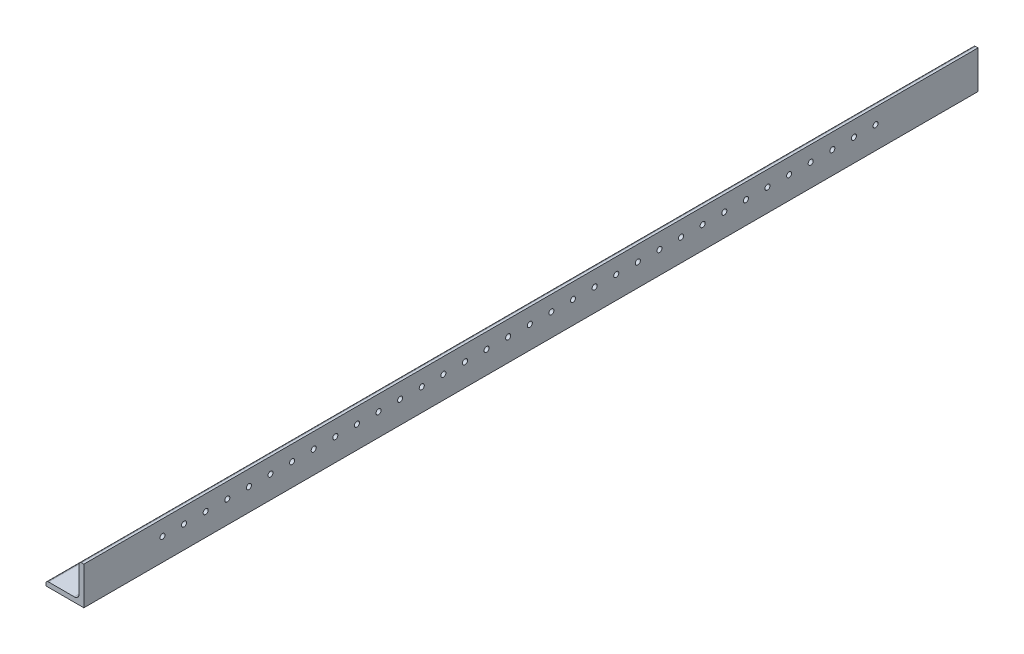
SolidWorks part; units mm, degrees
ref_plane "Front Plane" through (0, 0, 0) normal (0, 0, 1) x (1, 0, 0)
ref_plane "Top Plane" through (0, 0, 0) normal (0, 1, 0) x (1, 0, 0)
ref_plane "Right Plane" through (0, 0, 0) normal (1, 0, 0) x (0, 0, -1)
sketch "Sketch0" plane through (0, 0, 0) normal (0, 0, 1) x (1, 0, 0)
  line L0 (-12.7, -12.7) -> (12.7, -12.7)
  line L1 (12.7, -12.7) -> (12.7, 12.7)
  line L2 (12.7, 0) -> (0, 0) construction
  line L3 (0, 0) -> (0, -12.7) construction
  line L4 (9.525, -6.35) -> (9.525, 12.7) construction
  line L5 (6.35, -9.525) -> (-12.7, -9.525) construction
  arc A0 (9.525, -6.35) -> (6.35, -9.525) centre (6.35, -6.35) cw
  point P3 (8.5951, -8.5951)
  dimension "Inside Corner Radius" = 3.175
  dimension "Outside Height" = 25.4
  dimension "Inside Height" = 22.225
  dimension "Inside Width" = 22.225
  dimension "Wall Thickness" = 3.175
  dimension "D1" = 3.175
  dimension "Outside Width" = 25.4
sketch "Sketch1" plane through (0, 0, 0) normal (1, 0, 0) x (0, 0, -1)
  line L0 (609.6, 0) -> (-609.6, 0)
  point P4 (0, 0)
  dimension "Length" = 1219.2
sketch "Sketch2" plane through (0, 0, 0) normal (0, 0, 1) x (1, 0, 0)
  line L0 (-12.7, -12.7) -> (12.7, -12.7)
  line L1 (12.7, -12.7) -> (12.7, 12.7)
  line L2 (12.7, 12.7) -> (9.525, 12.7) construction
  line L3 (9.525, 11.1125) -> (9.525, -6.35)
  line L4 (6.35, -9.525) -> (-11.1125, -9.525)
  line L5 (-12.7, -12.7) -> (-12.7, -9.525) construction
  line L6 (11.1125, 12.7) -> (12.7, 12.7)
  line L7 (-12.7, -11.1125) -> (-12.7, -12.7)
  line L8 (12.7, 0) -> (0, 0) construction
  line L9 (0, 0) -> (0, -12.7) construction
  arc A0 (9.525, 11.1125) -> (11.1125, 12.7) centre (11.1125, 11.1125) cw
  arc A1 (-12.7, -11.1125) -> (-11.1125, -9.525) centre (-11.1125, -11.1125) cw
  arc A2 (9.525, -6.35) -> (6.35, -9.525) centre (6.35, -6.35) cw
  dimension "Inside Radius" = 3.175
  dimension "Height" = 25.4
  dimension "Width" = 25.4
  dimension "Thickness" = 3.175
extrude "Boss-Extrude1" add sketch "Sketch2" along normal mid plane 1219.2
sketch "Break Locations" plane through (0, 0, 0) normal (1, 0, 0) x (0, 0, -1)
  line L0 (-583.692, 0) -> (583.692, 0)
  line L1 (-609.6, -12.7) -> (-609.6, 12.7) construction
  line L2 (609.6, -12.7) -> (609.6, 12.7) construction
  point P0 (-588.01, 0)
  point P1 (588.01, 0)
  point P10 (0, 0)
  point P11 (583.692, 0)
  point P13 (-583.692, 0)
  dimension "D1" = 21.59
  dimension "D2" = 21.59
  dimension "D3" = 25.908
sketch "Sketch3" plane through (12.7, 0, 0) normal (1, 0, 0) x (0, 0, -1)
  line L0 (-609.6, -12.7) -> (609.6, -12.7) construction
  line L1 (609.6, 12.7) -> (-9.6, 12.7)
  line L2 (609.6, 12.7) -> (609.6, -12.7)
  line L3 (609.6, -12.7) -> (-9.6, -12.7)
  line L4 (-9.6, 12.7) -> (-9.6, -12.7)
  line L5 (-609.6, -12.7) -> (-609.6, 12.7) construction
  dimension "D1" = 600
extrude "Cut-Extrude2" cut sketch "Sketch3" against normal blind 30.48
sketch "Sketch5" plane through (9.525, 0, 0) normal (-1, 0, 0) x (0, 0, 1)
  line L0 (562.77, 11.1125) -> (562.77, -6.35) construction
  line L1 (609.6, 11.1125) -> (9.6, 11.1125) construction
  line L2 (609.6, 11.1125) -> (609.6, -6.35) construction
  line L3 (609.6, -6.35) -> (9.6, -6.35) construction
  line L4 (72.43, 11.1125) -> (72.43, -6.35) construction
  line L6 (72.43, 2.3812) -> (562.77, 2.3812) construction
  line L7 (78.35, 2.3812) -> (72.43, 2.3812)
  line L8 (556.85, 2.3812) -> (562.77, 2.3812)
  line L9 (72.43, 8.7325) -> (72.43, -3.9675) construction
  circle A0 centre (78.35, 2.3812) radius 1.7
  circle A1 centre (92.85, 2.3812) radius 1.7
  circle A2 centre (107.35, 2.3812) radius 1.7
  circle A3 centre (121.85, 2.3812) radius 1.7
  circle A4 centre (136.35, 2.3812) radius 1.7
  circle A5 centre (150.85, 2.3812) radius 1.7
  circle A6 centre (165.35, 2.3812) radius 1.7
  circle A7 centre (179.85, 2.3812) radius 1.7
  circle A8 centre (194.35, 2.3812) radius 1.7
  circle A9 centre (208.85, 2.3812) radius 1.7
  circle A10 centre (223.35, 2.3812) radius 1.7
  circle A11 centre (237.85, 2.3812) radius 1.7
  circle A12 centre (252.35, 2.3812) radius 1.7
  circle A13 centre (266.85, 2.3812) radius 1.7
  circle A14 centre (281.35, 2.3812) radius 1.7
  circle A15 centre (295.85, 2.3812) radius 1.7
  circle A16 centre (310.35, 2.3812) radius 1.7
  circle A17 centre (324.85, 2.3812) radius 1.7
  circle A18 centre (339.35, 2.3812) radius 1.7
  circle A19 centre (353.85, 2.3812) radius 1.7
  circle A20 centre (368.35, 2.3812) radius 1.7
  circle A21 centre (382.85, 2.3812) radius 1.7
  circle A22 centre (397.35, 2.3812) radius 1.7
  circle A23 centre (411.85, 2.3812) radius 1.7
  circle A24 centre (426.35, 2.3812) radius 1.7
  circle A25 centre (440.85, 2.3812) radius 1.7
  circle A26 centre (455.35, 2.3812) radius 1.7
  circle A27 centre (469.85, 2.3812) radius 1.7
  circle A28 centre (484.35, 2.3812) radius 1.7
  circle A29 centre (498.85, 2.3812) radius 1.7
  circle A30 centre (513.35, 2.3812) radius 1.7
  circle A31 centre (527.85, 2.3812) radius 1.7
  circle A32 centre (542.35, 2.3812) radius 1.7
  circle A33 centre (556.85, 2.3812) radius 1.7
  dimension "D1" = 3.4
  dimension "D3" = 14.5
  dimension "D4" = 46.83
  dimension "D2" = 34
extrude "Cut-Extrude3" cut sketch "Sketch5" against normal through all
sketch "Sketch7" plane through (0, -9.525, 0) normal (0, 1, 0) x (1, 0, 0)
  line L0 (-11.1125, -562.7675) -> (6.35, -562.7675) construction
  line L1 (-11.1125, -609.6) -> (-11.1125, -9.6) construction
  line L2 (-2.3812, -556.85) -> (-2.3812, -562.7675)
  line L3 (6.35, -609.6) -> (6.35, -9.6) construction
  line L5 (-2.3812, -72.4325) -> (-2.3812, -562.7675) construction
  line L6 (-2.3812, -78.35) -> (-2.3812, -72.4325)
  line L8 (-8.7325, -562.7675) -> (3.9675, -562.7675) construction
  line L9 (3.9675, -72.4325) -> (-8.7325, -72.4325) construction
  circle A0 centre (-2.3812, -78.35) radius 1.7
  circle A1 centre (-2.3812, -92.85) radius 1.7
  circle A2 centre (-2.3812, -107.35) radius 1.7
  circle A3 centre (-2.3812, -121.85) radius 1.7
  circle A4 centre (-2.3812, -136.35) radius 1.7
  circle A5 centre (-2.3812, -150.85) radius 1.7
  circle A6 centre (-2.3812, -165.35) radius 1.7
  circle A7 centre (-2.3812, -179.85) radius 1.7
  circle A8 centre (-2.3812, -194.35) radius 1.7
  circle A9 centre (-2.3812, -208.85) radius 1.7
  circle A10 centre (-2.3812, -223.35) radius 1.7
  circle A11 centre (-2.3812, -237.85) radius 1.7
  circle A12 centre (-2.3812, -252.35) radius 1.7
  circle A13 centre (-2.3812, -266.85) radius 1.7
  circle A14 centre (-2.3812, -281.35) radius 1.7
  circle A15 centre (-2.3812, -295.85) radius 1.7
  circle A16 centre (-2.3812, -310.35) radius 1.7
  circle A17 centre (-2.3812, -324.85) radius 1.7
  circle A18 centre (-2.3812, -339.35) radius 1.7
  circle A19 centre (-2.3812, -353.85) radius 1.7
  circle A20 centre (-2.3812, -368.35) radius 1.7
  circle A21 centre (-2.3812, -382.85) radius 1.7
  circle A22 centre (-2.3812, -397.35) radius 1.7
  circle A23 centre (-2.3812, -411.85) radius 1.7
  circle A24 centre (-2.3812, -426.35) radius 1.7
  circle A25 centre (-2.3812, -440.85) radius 1.7
  circle A26 centre (-2.3812, -455.35) radius 1.7
  circle A27 centre (-2.3812, -469.85) radius 1.7
  circle A28 centre (-2.3812, -484.35) radius 1.7
  circle A29 centre (-2.3812, -498.85) radius 1.7
  circle A30 centre (-2.3812, -513.35) radius 1.7
  circle A31 centre (-2.3812, -527.85) radius 1.7
  circle A32 centre (-2.3812, -542.35) radius 1.7
  circle A33 centre (-2.3812, -556.85) radius 1.7
  dimension "D2" = 3.4
  dimension "D3" = 14.5
  dimension "D1" = 34
extrude "Cut-Extrude4" cut sketch "Sketch7" against normal through all
equation "\"D1@Break Locations\" = .85 * \"Height@Sketch2\""
equation "\"D2@Break Locations\"=\"D1@Break Locations\""
equation "\"Thickness@Sketch2\" = \"Wall Thickness@Sketch0\""
equation "\"Height@Sketch2\" = \"Outside Height@Sketch0\""
equation "\"Width@Sketch2\" = \"Outside Width@Sketch0\""
equation "\"Inside Radius@Sketch2\" = \"Inside Corner Radius@Sketch0\""
equation "\"Length@Boss-Extrude1\" = \"Length@Sketch1\""
equation "\"D3@Break Locations\"=\"D2@Break Locations\"*1.2"
equation "\"D1@Sketch0\"=\"Wall Thickness@Sketch0\""
